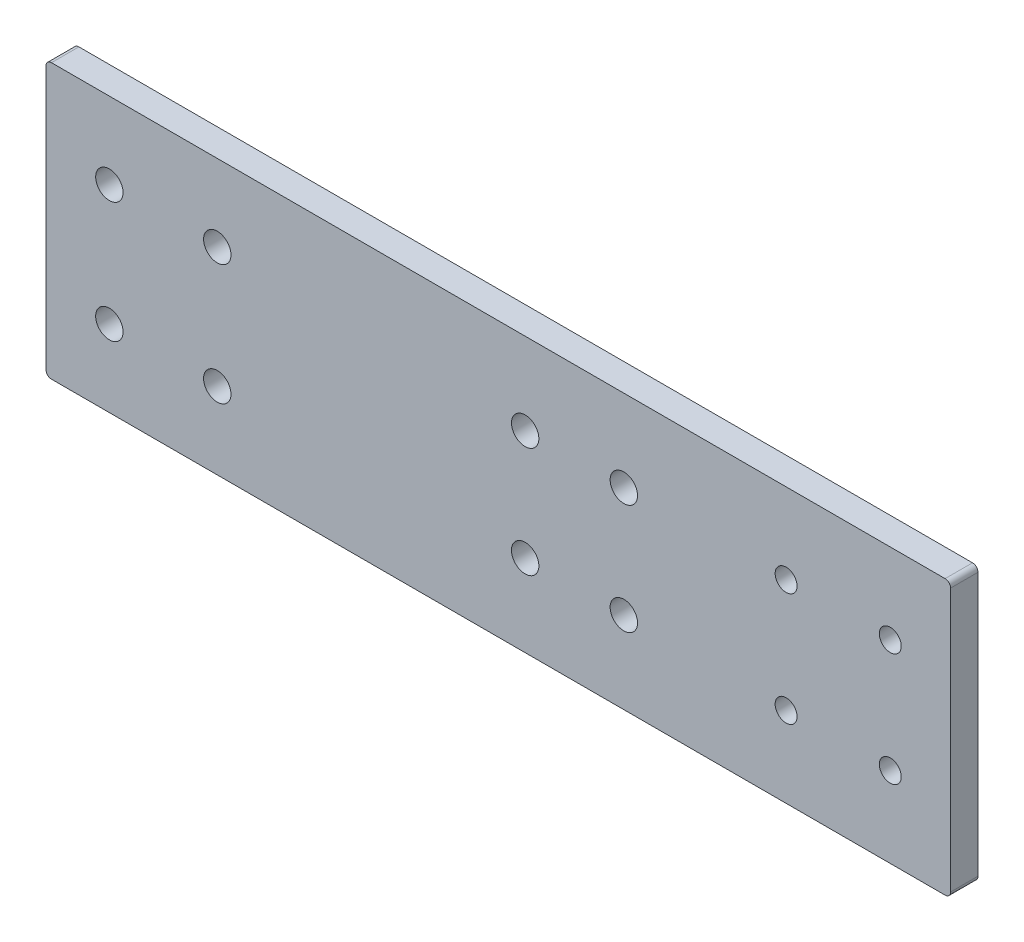
SolidWorks part; units mm, degrees
ref_plane "Piano frontale" through (0, 0, 0) normal (0, 0, 1) x (1, 0, 0)
ref_plane "Piano superiore" through (0, 0, 0) normal (0, 1, 0) x (1, 0, 0)
ref_plane "Piano destro" through (0, 0, 0) normal (1, 0, 0) x (0, 0, -1)
sketch "Sketch1" plane through (0, 0, 0) normal (0, 0, 1) x (1, 0, 0)
  line L0 (0, 25) -> (165, 25) construction
  line L1 (1, 0) -> (164, 0)
  line L2 (0, 1) -> (0, 49)
  line L3 (1, 50) -> (164, 50)
  line L4 (165, 1) -> (165, 49)
  line L5 (96.4, 25) -> (96.4, 44) construction
  line L6 (127, 44) -> (127, 6) construction
  line L7 (121, 6) -> (162, 6) construction
  line L8 (121, 6) -> (121, 44) construction
  line L9 (121, 44) -> (162, 44) construction
  line L10 (162, 6) -> (162, 44) construction
  line L11 (70.4, 44) -> (113.4, 44) construction
  line L12 (70.4, 44) -> (70.4, 6) construction
  line L13 (70.4, 6) -> (113.4, 6) construction
  line L14 (113.4, 44) -> (113.4, 6) construction
  line L15 (4.4, 44) -> (47.4, 44) construction
  line L16 (4.4, 44) -> (4.4, 6) construction
  line L17 (4.4, 6) -> (47.4, 6) construction
  line L18 (47.4, 44) -> (47.4, 6) construction
  line L19 (127, 44) -> (162, 6) construction
  line L20 (127, 6) -> (162, 44) construction
  line L21 (144.5, 25) -> (144.5, 44) construction
  line L22 (79.4, 44) -> (79.4, 6) construction
  line L23 (79.4, 44) -> (113.4, 6) construction
  line L24 (113.4, 44) -> (79.4, 6) construction
  line L25 (38.4, 44) -> (38.4, 6) construction
  line L26 (4.4, 44) -> (38.4, 6) construction
  line L27 (38.4, 44) -> (4.4, 6) construction
  line L28 (21.4, 25) -> (21.4, 44) construction
  arc A4 (0, 49) -> (1, 50) centre (1, 49) cw
  arc A5 (164, 0) -> (165, 1) centre (164, 1) ccw
  arc A6 (1, 0) -> (0, 1) centre (1, 1) cw
  arc A7 (164, 50) -> (165, 49) centre (164, 49) cw
  circle A8 centre (135, 35.3143) radius 2
  circle A9 centre (135, 14.6857) radius 2
  circle A10 centre (154, 14.6857) radius 2
  circle A11 centre (154, 35.3143) radius 2
  circle A12 centre (105.4, 35.0588) radius 2.5
  circle A13 centre (105.4, 14.9412) radius 2.5
  circle A14 centre (87.4, 14.9412) radius 2.5
  circle A15 centre (87.4, 35.0588) radius 2.5
  circle A16 centre (11.5579, 36) radius 2.5
  circle A17 centre (11.5579, 14) radius 2.5
  circle A18 centre (31.2421, 14) radius 2.5
  circle A19 centre (31.2421, 36) radius 2.5
  point P13 (0, 50)
  point P16 (165, 0)
  point P20 (0, 0)
  point P23 (165, 50)
  point P35 (144.5, 25)
  point P46 (96.4, 25)
  dimension "D3" = 1
  dimension "D4" = 41
  dimension "D8" = 4
  dimension "D13" = 5
  dimension "D18" = 5
  dimension "D1" = 165
  dimension "D2" = 50
  dimension "D5" = 38
  dimension "D6" = 35
  dimension "D7" = 3
  dimension "D9" = 8
  dimension "D10" = 9
  dimension "D11" = 43
  dimension "D12" = 41.6
  dimension "D14" = 8
  dimension "D15" = 23
  dimension "D16" = 43
  dimension "D17" = 34
  dimension "D19" = 8
extrude "Boss-Extrude1" add sketch "Sketch1" along normal blind 5
